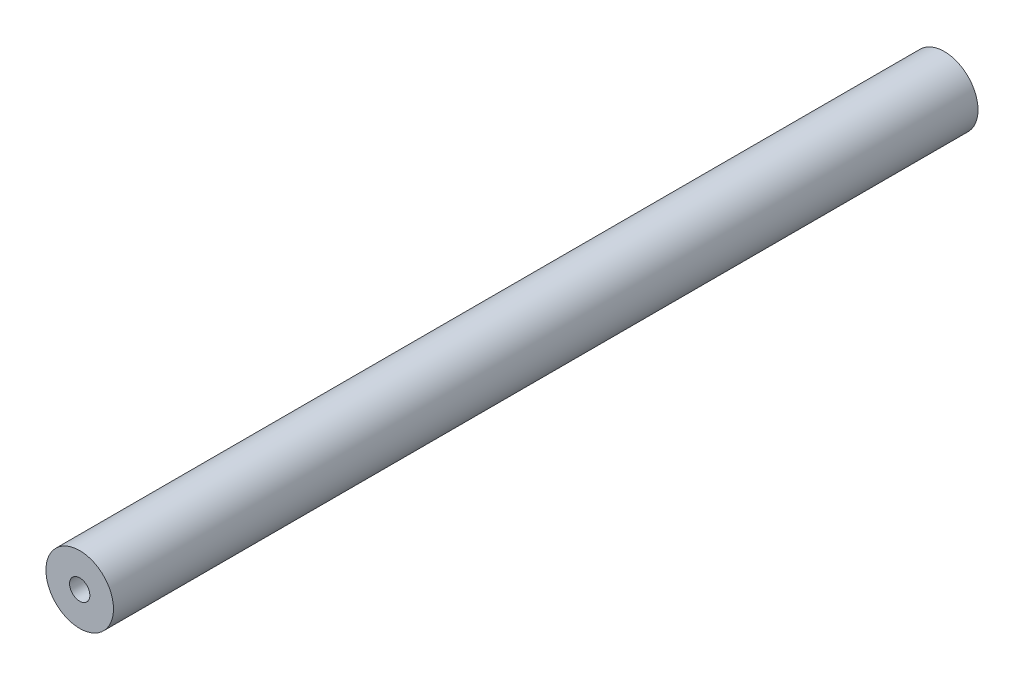
SolidWorks part; units mm, degrees
ref_plane "Front Plane" through (0, 0, 0) normal (0, 0, 1) x (1, 0, 0)
ref_plane "Top Plane" through (0, 0, 0) normal (0, 1, 0) x (1, 0, 0)
ref_plane "Right Plane" through (0, 0, 0) normal (1, 0, 0) x (0, 0, -1)
sketch "Sketch1" plane through (0, 0, 0) normal (0, 0, 1) x (1, 0, 0)
  circle A0 centre (0, 0) radius 31.75
  circle A1 centre (0, 0) radius 9.525
  dimension "D1" = 63.5
  dimension "D2" = 19.05
extrude "Boss-Extrude1" add sketch "Sketch1" along normal blind 812.8
